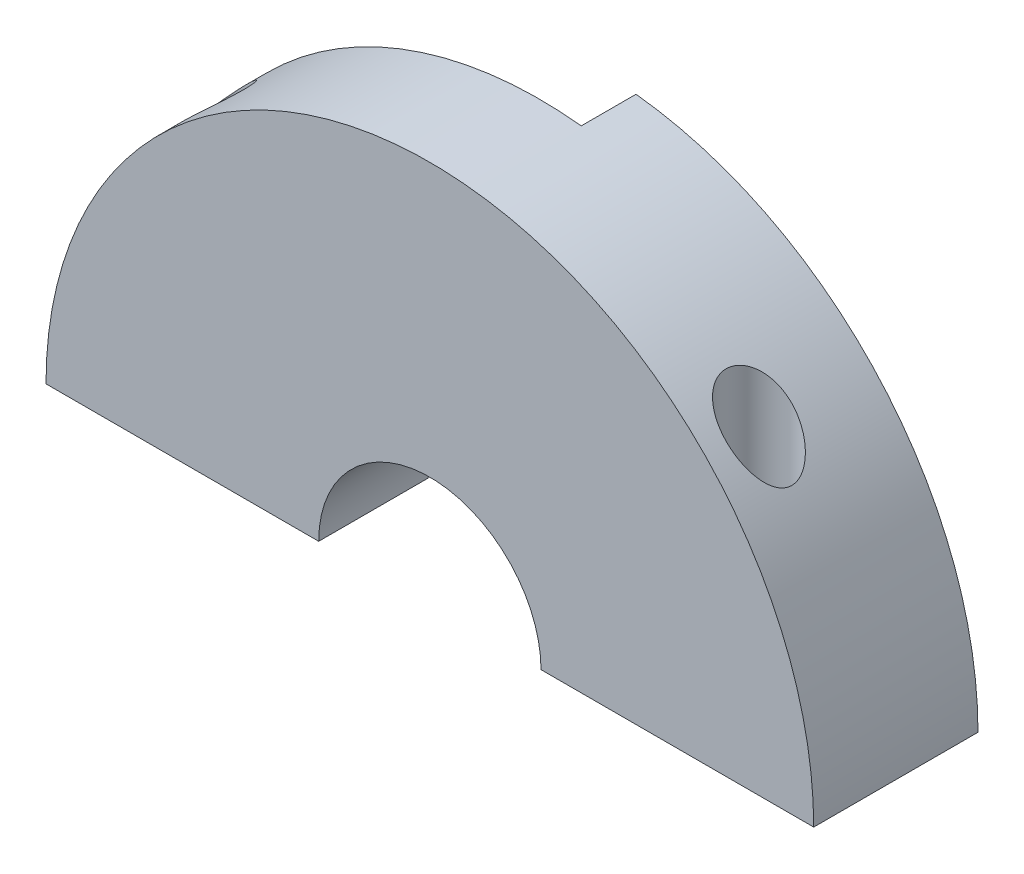
SolidWorks part; units mm, degrees
ref_plane "Front Plane" through (0, 0, 0) normal (0, 0, 1) x (1, 0, 0)
ref_plane "Top Plane" through (0, 0, 0) normal (0, 1, 0) x (1, 0, 0)
ref_plane "Right Plane" through (0, 0, 0) normal (1, 0, 0) x (0, 0, -1)
sketch "Sketch1" plane through (0, 0, 0) normal (0, 0, 1) x (1, 0, 0)
  line L0 (-35.05, 0) -> (-10.15, 0)
  line L1 (10.15, 0) -> (35.05, 0)
  arc A0 (-10.15, 0) -> (10.15, 0) centre (0, 0) cw
  arc A1 (-35.05, 0) -> (35.05, 0) centre (0, 0) cw
  dimension "D1" = 10.15
  dimension "D2" = 24.9
extrude "Boss-Extrude1" add sketch "Sketch1" along normal mid plane 10
sketch "Sketch2" plane through (0, 0, 0) normal (0, 1, 0) x (1, 0, 0)
  line L0 (-35.05, -5) -> (-35.05, 5) construction
  circle A0 centre (-25.05, 0) radius 1.7
  dimension "D1" = 3.4
  dimension "D2" = 10
extrude "Cut-Extrude1" cut sketch "Sketch2" along normal through all
sketch "Sketch3" plane through (0, 0, 0) normal (0, 1, 0) x (1, 0, 0)
  circle A0 centre (-25.05, 0) radius 3
  dimension "D1" = 6
extrude "Cut-Extrude2" cut sketch "Sketch3" along normal through all from offset 2
mirror "Mirror1" about plane through (0, 0, 0) normal (1, 0, 0) of "Cut-Extrude1", "Cut-Extrude2"
sketch "Sketch4" plane through (0, 0, 5) normal (0, 0, 1) x (1, 0, 0)
  line L0 (0, 12.5) -> (0, 35.05)
  line L1 (10.15, 0) -> (35.05, 0) construction
  line L2 (12.5, 0) -> (35.05, 0)
  arc A0 (35.05, 0) -> (-35.05, 0) centre (0, 0) ccw construction
  arc A1 (0, 12.5) -> (12.5, 0) centre (0, 0) cw
  arc A2 (35.05, 0) -> (0, 35.05) centre (0, 0) ccw
  dimension "D1" = 12.5
extrude "Boss-Extrude2" add sketch "Sketch4" along normal blind 5
sketch "Sketch5" plane through (0, 0, 5) normal (0, 0, 1) x (1, 0, 0)
  line L1 (0, 10.15) -> (3.825, 10.15)
  line L2 (0, 10.15) -> (0, 35.05)
  line L3 (0, 35.05) -> (3.825, 35.05)
  line L4 (3.825, 10.15) -> (3.825, 35.05)
  arc A0 (10.15, 0) -> (-10.15, 0) centre (0, 0) ccw construction
  dimension "D1" = 3.825
extrude "Cut-Extrude3" cut sketch "Sketch5" along normal through all
mirror "Mirror2" about plane through (0, 0, 0) normal (0, 0, 1) of "Cut-Extrude3", "Boss-Extrude2"
sketch "Sketch6" plane through (3.825, 0, 0) normal (-1, 0, 0) x (0, 0, 1)
  line L1 (10, 0) -> (5, 0)
  line L2 (10, 0) -> (10, 34.8407)
  line L3 (10, 34.8407) -> (5, 34.8407)
  line L4 (5, 0) -> (5, 34.8407)
extrude "Cut-Extrude4" cut sketch "Sketch6" against normal through all
